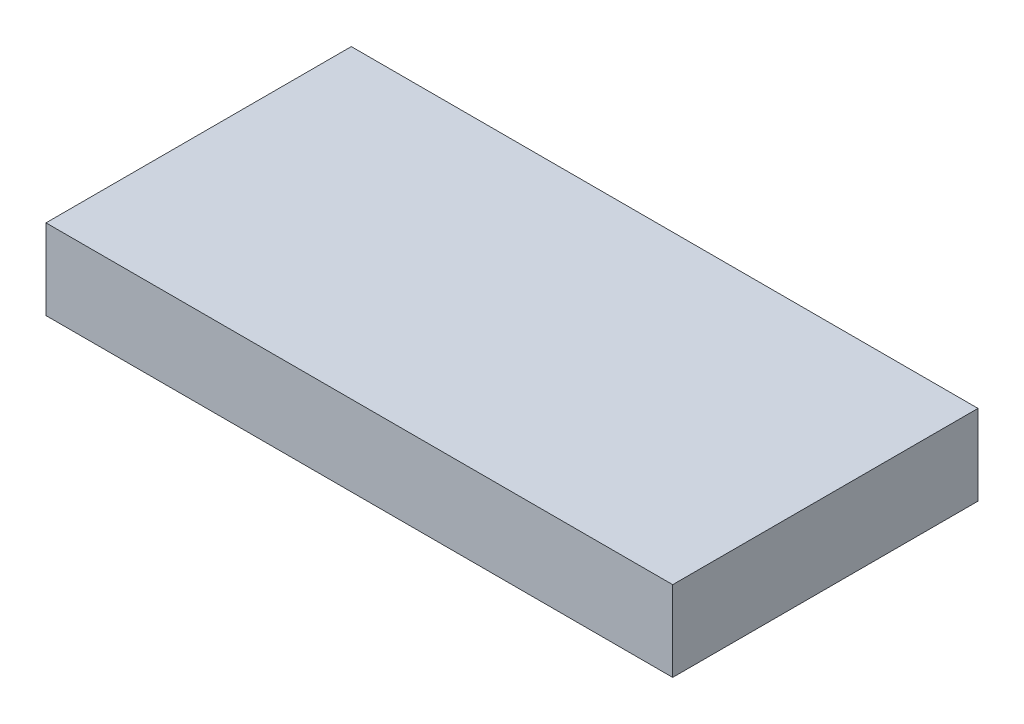
SolidWorks part; units mm, degrees
ref_plane "Front Plane" through (0, 0, 0) normal (0, 0, 1) x (1, 0, 0)
ref_plane "Top Plane" through (0, 0, 0) normal (0, 1, 0) x (1, 0, 0)
ref_plane "Right Plane" through (0, 0, 0) normal (1, 0, 0) x (0, 0, -1)
sketch "Sketch1" plane through (0, 0, 0) normal (0, 1, 0) x (1, 0, 0)
  line L1 (-19.5, -9.5) -> (19.5, -9.5)
  line L2 (-19.5, -9.5) -> (-19.5, 9.5)
  line L3 (-19.5, 9.5) -> (19.5, 9.5)
  line L4 (19.5, -9.5) -> (19.5, 9.5)
  line L5 (-19.5, -9.5) -> (19.5, 9.5) construction
  line L6 (-19.5, 9.5) -> (19.5, -9.5) construction
  point P0 (0, 0)
  dimension "D1" = 39
  dimension "D2" = 19
extrude "Boss-Extrude1" add sketch "Sketch1" along normal blind 5
